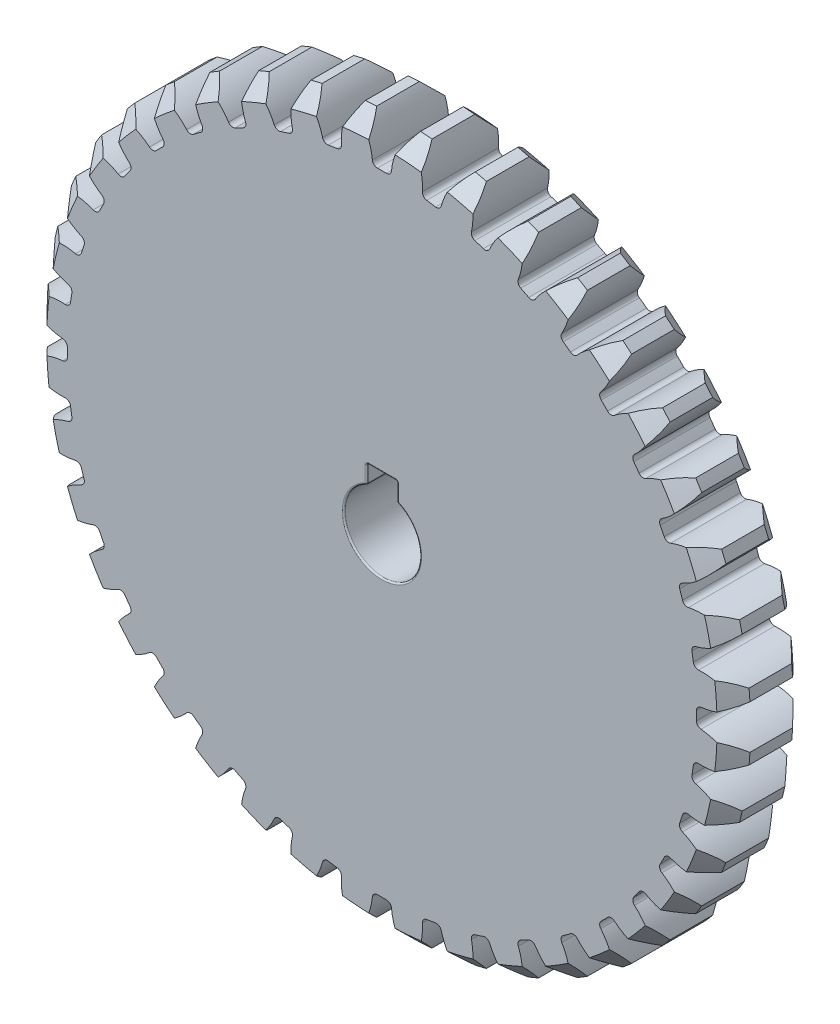
SolidWorks part; units mm, degrees
ref_plane "Front Plane" through (0, 0, 0) normal (0, 0, 1) x (1, 0, 0)
ref_plane "Top Plane" through (0, 0, 0) normal (0, 1, 0) x (1, 0, 0)
ref_plane "Right Plane" through (0, 0, 0) normal (1, 0, 0) x (0, 0, -1)
sketch "Sketch1" plane through (0, 0, 0) normal (0, 0, 1) x (1, 0, 0)
  circle A0 centre (0, 0) radius 44 construction
  circle A1 centre (0, 0) radius 46.2
  dimension "D1" = 88
  dimension "D2" = 92.4
extrude "Boss-Extrude1" add sketch "Sketch1" along normal mid plane 10
sketch "Sketch2" plane through (0, 0, 0) normal (0, 0, 1) x (1, 0, 0)
  line L0 (0, 0) -> (0, 46.2) construction
  line L1 (0, 0) -> (7.2273, 45.6312) construction
  line L2 (0, 0) -> (3.6248, 46.0576) construction
  line L3 (-1.2134, 41.2822) -> (0, 0) construction
  line L4 (-1.7274, 43.9661) -> (1.7274, 43.9661) construction
  line L5 (1.7274, 43.9661) -> (5.1716, 43.695) construction
  line L6 (-2.5156, 46.1315) -> (0, 39.22) construction
  circle A0 centre (0, 0) radius 41.8 construction
  circle A2 centre (0, 0) radius 46.2 construction
  arc A3 (-2.8745, 46.1105) -> (-1.2134, 41.2822) centre (-9.7944, 41.0299) cw
  circle A4 centre (0, 0) radius 46.2 construction
  arc A5 (2.8745, 46.1105) -> (1.2134, 41.2822) centre (9.7944, 41.0299) ccw
  circle A6 centre (0, 0) radius 44 construction
  arc A7 (1.2134, 41.2822) -> (-1.2134, 41.2822) centre (0, 0) ccw
  arc A8 (2.8745, 46.1105) -> (-2.8745, 46.1105) centre (0, 0) ccw
  dimension "D1" = 9
  dimension "D2" = 4.4
  dimension "D4" = 20
  dimension "D3" = 0.5
extrude "Cut-Extrude1" cut sketch "Sketch2" against normal through all both and the other way through all contours A5 A8 A3 A7
fillet "Fillet1" radius 0.66 2 edges at (1.2134, 41.2822, 0) (-1.2134, 41.2822, 0)
chamfer "Chamfer1" distance 2.2 angle 45 2 edges at (0, -46.2, -5) (0, -46.2, 5)
pattern_circular "CirPattern1" count 40 over 360 about axis through (0, 0, 0) along (0, 0, 1) of "Fillet1", "Cut-Extrude1"
sketch "Sketch3" plane through (0, 0, 5) normal (0, 0, 1) x (1, 0, 0)
  line L2 (-2, 4.5826) -> (-2, 7)
  line L3 (-2, 7) -> (2, 7)
  line L4 (2, 4.5826) -> (2, 7)
  arc A0 (-2, 4.5826) -> (2, 4.5826) centre (0, 0) ccw
  point P3 (0, 5)
  point P5 (0, 7)
  dimension "D1" = 10
  dimension "D2" = 2
  dimension "D3" = 4
extrude "Cut-Extrude2" cut sketch "Sketch3" against normal through all
fillet "Fillet2" radius 0.2 12 edges at (0, -5, 5) (0, -5, -5) (-2, 4.5826, 0) (2, 4.5826, 0) (0, 7, -5) (0, 7, 5) (-2, 7, 0) (-2, 5.7913, -5) (-2, 5.7913, 5) (2, 5.7913, -5) (2, 7, 0) (2, 5.7913, 5)
sketch "Sketch4" plane through (0, 0, 0) normal (0, 0, 1) x (1, 0, 0)
  circle A0 centre (0, 0) radius 44
equation "\"Module\"= 2.2"
equation "\"Number of Teeth\"= 40'Number of Teeth"
equation "\"Pressure Angle\"= 20"
equation "\"D1@Sketch1\"=\"Module\" * \"Number of Teeth\""
equation "\"D2@Sketch1\"=( \"Number of Teeth\" + 2) * \"Module\""
equation "\"D1@Sketch2\"=360 / \"Number of Teeth\""
equation "\"D2@Sketch2\"= \"Module\" * 2"
equation "\"D4@Sketch2\"=\"Pressure Angle\""
equation "\"D1@Fillet1\"=0.3 * \"Module\""
equation "\"D1@CirPattern1\"= \"Number of Teeth\""
equation "\"D1@Chamfer1\"= \"Module\""
equation "\"Gear Thickness\"= 10"
equation "\"D1@Boss-Extrude1\"= \"Gear Thickness\""
